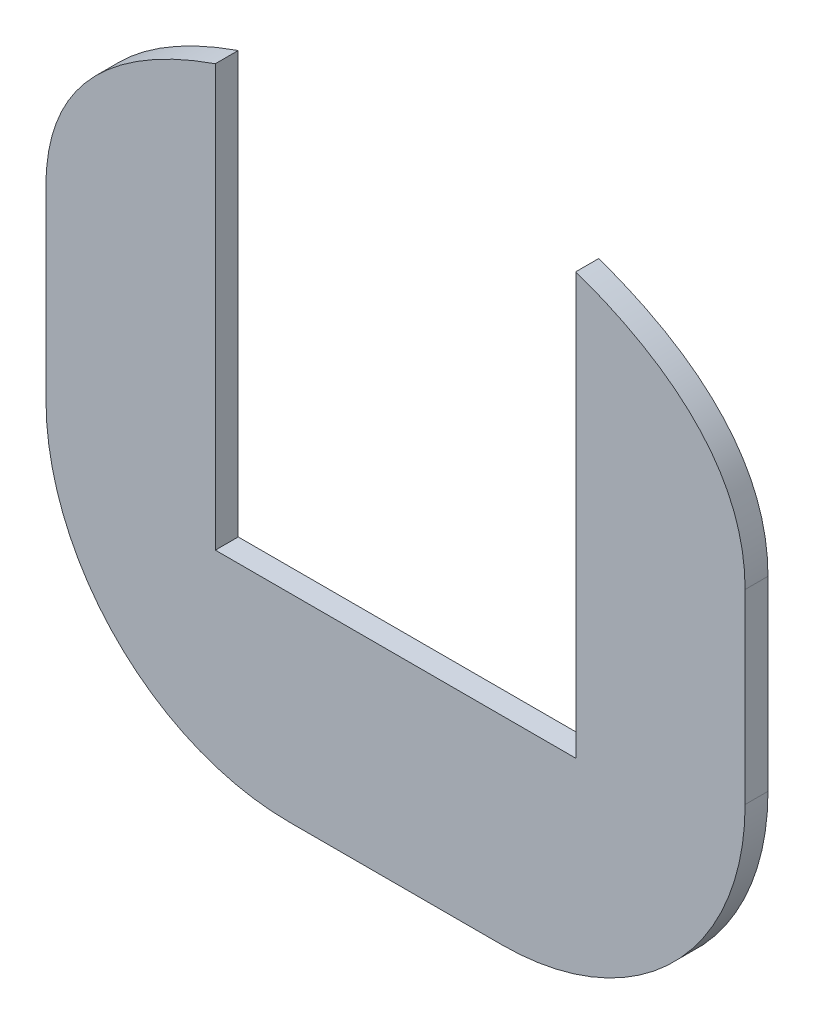
SolidWorks part; units mm, degrees
ref_plane "Front Plane" through (0, 0, 0) normal (0, 0, 1) x (1, 0, 0)
ref_plane "Top Plane" through (0, 0, 0) normal (0, 1, 0) x (1, 0, 0)
ref_plane "Right Plane" through (0, 0, 0) normal (1, 0, 0) x (0, 0, -1)
sketch "Sketch1" plane through (0, 0, 0) normal (0, 0, 1) x (1, 0, 0)
  line L0 (0, 33.5) -> (0, -96.5) construction
  line L1 (-70, 33.5) -> (70, 33.5) construction
  line L2 (-70, 33.5) -> (-70, -96.5) construction
  line L3 (-70, -96.5) -> (70, -96.5) construction
  line L4 (70, 33.5) -> (70, -96.5) construction
  line L5 (-25, 33.5) -> (25, 33.5) construction
  line L6 (-20, -96.5) -> (20, -96.5) construction
  line L7 (-70, -11.5) -> (70, -11.5) construction
  line L8 (-70, -11.5) -> (-70, -46.5) construction
  line L9 (-70, -46.5) -> (70, -46.5) construction
  line L10 (70, -11.5) -> (70, -46.5) construction
  line L11 (-10, 33.5) -> (10, 33.5) construction
  line L12 (-20, -96.5) -> (-14.4295, -96.5) construction
  line L13 (-14.4295, -96.5) -> (20, -96.5) construction
  line L14 (-70, -11.5) -> (-70, 26.5) construction
  line L15 (-70, 26.5) -> (-18, 33.5) construction
  line L16 (-18, 33.5) -> (-10, 33.5) construction
  line L17 (10, 33.5) -> (18, 33.5) construction
  line L18 (18, 33.5) -> (70, 26.5) construction
  line L19 (70, 26.5) -> (70, -11.5) construction
  line L20 (0, -55) -> (0, 55) construction
  line L21 (55, 0) -> (-55, 0) construction
  line L22 (-20, -92.2) -> (-14.4295, -92.2)
  line L23 (-14.4295, -92.2) -> (20, -92.2)
  line L24 (65.7, -11.5) -> (65.7, -46.5)
  line L25 (-10, 29.2) -> (10, 29.2)
  line L26 (-65.7, -11.5) -> (-65.7, -46.5)
  arc A0 (-70, -11.5) -> (-25, 33.5) centre (-25, -11.5) cw construction
  arc A1 (25, 33.5) -> (70, -11.5) centre (25, -11.5) cw construction
  arc A2 (-70, -46.5) -> (-20, -96.5) centre (-20, -46.5) ccw construction
  arc A3 (20, -96.5) -> (70, -46.5) centre (20, -46.5) ccw construction
  arc A4 (-65.7, -46.5) -> (-20, -92.2) centre (-20, -46.5) ccw
  arc A5 (20, -92.2) -> (65.7, -46.5) centre (20, -46.5) ccw
  spline S0 degree 3 poles (-70, -11.5) (-70, 26.5) (-18, 33.5) (-10, 33.5) knots 0 0 0 0 1 1 1 1 construction
  spline S1 degree 3 poles (10, 33.5) (18, 33.5) (70, 26.5) (70, -11.5) knots 0 0 0 0 1 1 1 1 construction
  spline S2 degree 1 poles (10, 29.2) (65.7, -11.5) knots 0 0 1 1 construction
  spline S3 degree 1 poles (-65.7, -11.5) (-10, 29.2) knots 0 0 1 1 construction
  spline S4 degree 3 poles (65.7, -11.5) (65.7, -10.9756) (65.6772, -9.9155) (65.5442, -7.8884) (65.2202, -5.4607) (64.5981, -2.7237) (63.4785, 0.7162) (61.5699, 4.6545) (58.5534, 8.8853) (54.8963, 12.6626) (49.3052, 17.1178) (41.2794, 21.6169) (32.8026, 24.7807) (26.3389, 26.6062) (21.7972, 27.6518) (17.7102, 28.4039) (14.8087, 28.8127) (12.8723, 29.0253) (11.6336, 29.1319) (10.8115, 29.1802) (10.283, 29.1976) (10.1012, 29.2) (10, 29.2) knots 0 0 0 0 0.015625 0.03125 0.0625 0.09375 0.125 0.1875 0.25 0.3125 0.375 0.5 0.625 0.6875 0.75 0.8125 0.875 0.90625 0.9375 0.96875 0.984375 1 1 1 1
  spline S5 degree 3 poles (-10, 29.2) (-10.1012, 29.2) (-10.283, 29.1976) (-10.8115, 29.1802) (-11.6336, 29.1319) (-12.8723, 29.0253) (-14.8087, 28.8127) (-17.7102, 28.4039) (-21.7972, 27.6518) (-26.3389, 26.6062) (-32.8026, 24.7807) (-41.2794, 21.6169) (-49.3052, 17.1178) (-54.8963, 12.6626) (-58.5534, 8.8853) (-61.5699, 4.6545) (-63.4785, 0.7162) (-64.5981, -2.7237) (-65.2202, -5.4607) (-65.5442, -7.8884) (-65.6772, -9.9155) (-65.7, -10.9756) (-65.7, -11.5) knots 0 0 0 0 0.015625 0.03125 0.0625 0.09375 0.125 0.1875 0.25 0.3125 0.375 0.5 0.625 0.6875 0.75 0.8125 0.875 0.90625 0.9375 0.96875 0.984375 1 1 1 1
  point P10 (0, 33.5)
  point P19 (0, -96.5)
  point P24 (0, 33.5)
  dimension "D3" = 50
  dimension "D1" = 130
  dimension "D2" = 140
  dimension "D4" = 20
  dimension "D5" = 45
  dimension "D6" = 38
  dimension "D7" = 52
  dimension "D8" = 52
  dimension "D9" = 38
  dimension "D10" = 11.5
  dimension "D11" = 4.3
extrude "Boss-Extrude1" add sketch "Sketch1" along normal blind 4.3
sketch "Sketch2" plane through (0, 0, 4.3) normal (0, 0, 1) x (1, 0, 0)
  line L0 (0, -2.365) -> (0, 2.365) construction
  line L1 (-33.87, 24.2997) -> (33.87, 24.2997) construction
  line L2 (-33.87, 24.2997) -> (-33.87, -54.8803)
  line L3 (-33.87, -54.8803) -> (33.87, -54.8803)
  line L4 (33.87, 24.2997) -> (33.87, -54.8803)
  line L6 (-33.87, 24.2997) -> (33.87, 24.2997) construction
  line L7 (-33.87, 24.2997) -> (-33.87, 35.4689)
  line L8 (-33.87, 35.4689) -> (33.87, 35.4689)
  line L9 (33.87, 24.2997) -> (33.87, 35.4689)
  spline S0 degree 3 poles (65.7, -11.5) (65.7, -10.9756) (65.6772, -9.9155) (65.5442, -7.8884) (65.2202, -5.4607) (64.5981, -2.7237) (63.4785, 0.7162) (61.5699, 4.6545) (58.5534, 8.8853) (54.8963, 12.6626) (49.3052, 17.1178) (41.2794, 21.6169) (32.8026, 24.7807) (26.3389, 26.6062) (21.7972, 27.6518) (17.7102, 28.4039) (14.8087, 28.8127) (12.8723, 29.0253) (11.6336, 29.1319) (10.8115, 29.1802) (10.283, 29.1976) (10.1012, 29.2) (10, 29.2) knots 0 0 0 0 0.015625 0.03125 0.0625 0.09375 0.125 0.1875 0.25 0.3125 0.375 0.5 0.625 0.6875 0.75 0.8125 0.875 0.90625 0.9375 0.96875 0.984375 1 1 1 1 construction
  point P4 (0, -54.8803)
  point P7 (-33.87, 24.2997)
  dimension "D1" = 67.74
  dimension "D2" = 79.18
extrude "Cut-Extrude1" cut sketch "Sketch2" against normal blind 10
